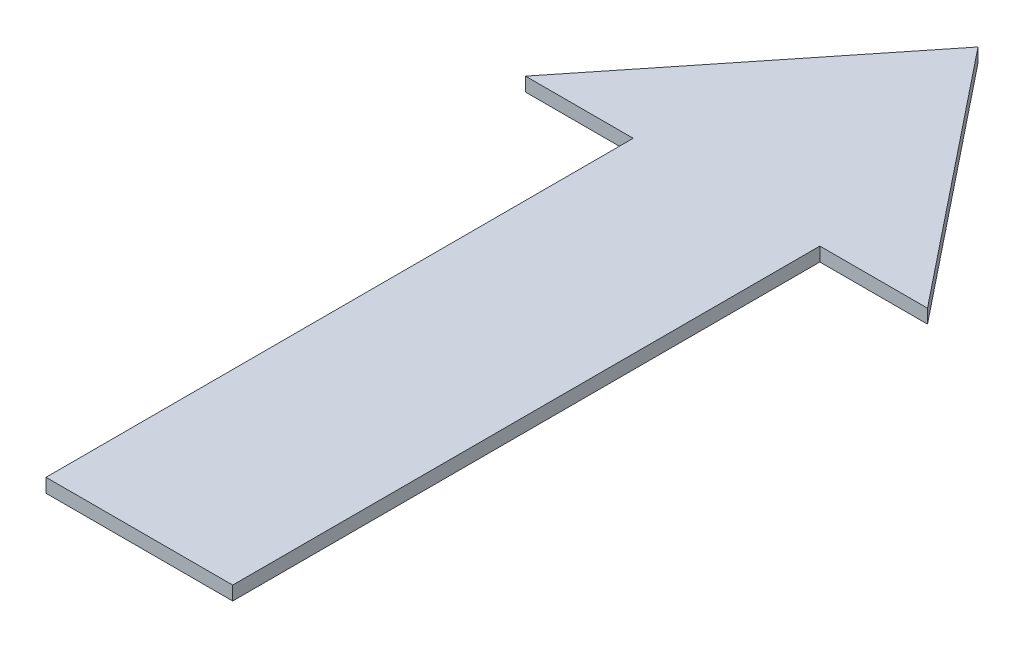
SolidWorks part; units mm, degrees
ref_plane "Front Plane" through (0, 0, 0) normal (0, 0, 1) x (1, 0, 0)
ref_plane "Top Plane" through (0, 0, 0) normal (0, 1, 0) x (1, 0, 0)
ref_plane "Right Plane" through (0, 0, 0) normal (1, 0, 0) x (0, 0, -1)
sketch "Sketch1" plane through (0, 0, 0) normal (0, 1, 0) x (1, 0, 0)
  line L0 (0, 0) -> (0, 42.4464)
  line L1 (0, 42.4464) -> (-7.7811, 42.4464)
  line L2 (-7.7811, 42.4464) -> (6.7476, 60.6257)
  line L3 (6.7476, 60.6257) -> (21.2762, 42.4464)
  line L4 (21.2762, 42.4464) -> (13.4951, 42.4464)
  line L5 (13.4951, 42.4464) -> (13.4951, 0)
  line L6 (13.4951, 0) -> (0, 0)
  line L7 (6.7476, 60.6257) -> (6.7476, 0) construction
  point P3 (6.7476, 60.6257)
  dimension "D1" = 42.4464
  dimension "D2" = 23.2717
  dimension "D3" = 13.4951
  dimension "D4" = 18.1794
extrude "Boss-Extrude1" add sketch "Sketch1" along normal blind 1
